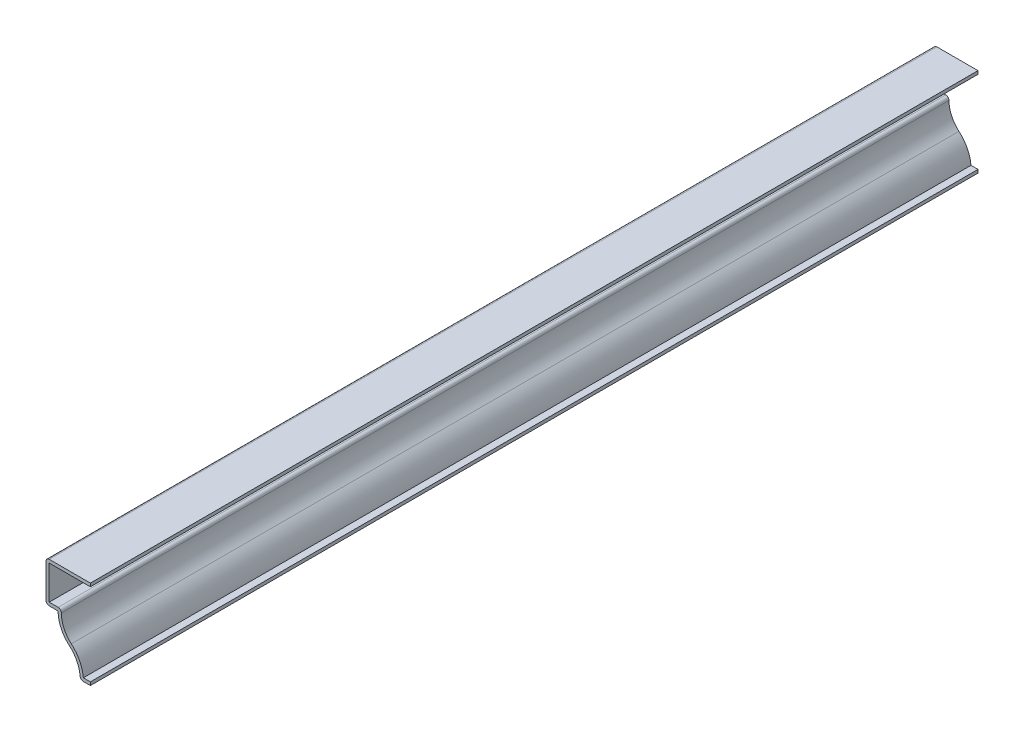
SolidWorks part; units mm, degrees
ref_plane "Front Plane" through (0, 0, 0) normal (0, 0, 1) x (1, 0, 0)
ref_plane "Top Plane" through (0, 0, 0) normal (0, 1, 0) x (1, 0, 0)
ref_plane "Right Plane" through (0, 0, 0) normal (1, 0, 0) x (0, 0, -1)
sketch "Sketch1" plane through (0, 0, 0) normal (0, 0, 1) x (1, 0, 0)
  line L0 (0, 0) -> (0, 34.925) construction
  line L1 (0, 34.925) -> (-17.4625, 34.925)
  line L2 (-17.4625, 34.925) -> (-17.4625, 19.05)
  line L3 (-17.4625, 19.05) -> (-12.7, 19.05)
  line L4 (0, 0) -> (-3.9688, 0)
  line L5 (-3.9688, 0) -> (-20.9528, 0) construction
  line L6 (-17.4625, 19.05) -> (-17.4625, 0) construction
  arc A0 (-12.7, 19.05) -> (-8.3344, 9.525) centre (-0.1263, 19.05) ccw
  arc A1 (-8.3344, 9.525) -> (-3.9688, 0) centre (-16.5425, 0) cw
  point P10 (-17.4625, 9.525)
  point P13 (-8.3344, 9.525)
  point P14 (0, 0)
  dimension "D1" = 3.9688
  dimension "D2" = 4.7625
  dimension "D3" = 8.7312
  dimension "D4" = 34.925
  dimension "D5" = 15.875
extrude "Extrude-Thin1" add sketch "Sketch1" against normal blind 349.25 thin thin type one direction reverse wall 1.27
fillet "Fillet1" radius 1.27 4 edges at (-3.9688, 0, -174.625) (-11.3584, 20.32, -174.625) (-17.4625, 19.05, -174.625) (-17.4625, 34.925, -174.625)
